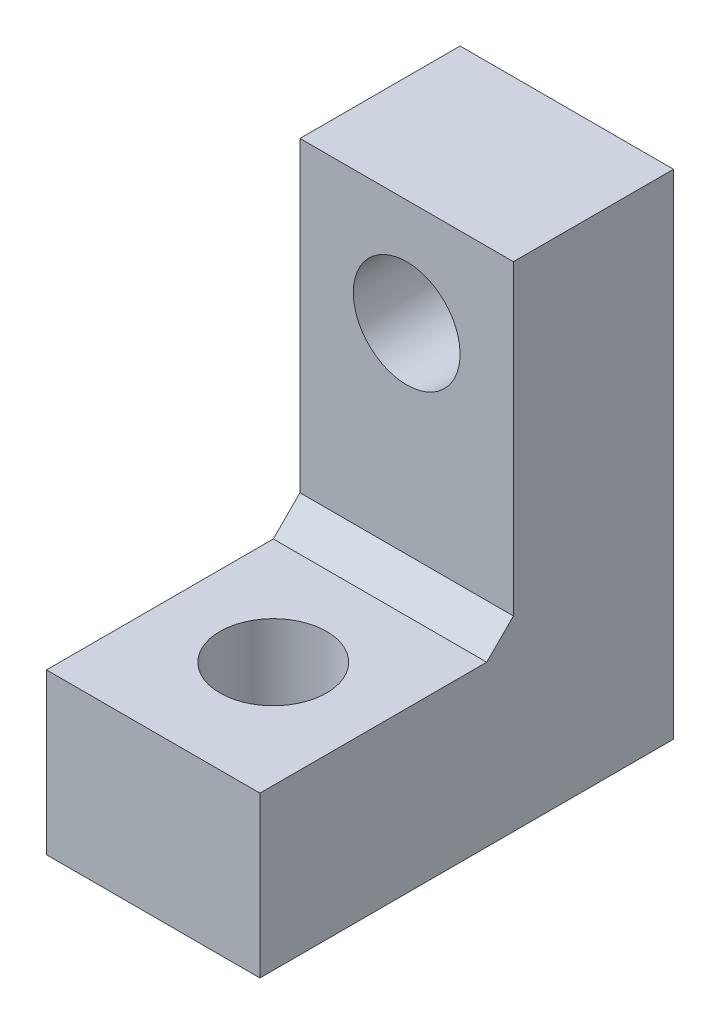
SolidWorks part; units mm, degrees
material "ABS"
ref_plane "Front Plane" through (0, 0, 0) normal (0, 0, 1) x (1, 0, 0)
ref_plane "Top Plane" through (0, 0, 0) normal (0, 1, 0) x (1, 0, 0)
ref_plane "Right Plane" through (0, 0, 0) normal (1, 0, 0) x (0, 0, -1)
sketch "Sketch1" plane through (0, 0, 0) normal (1, 0, 0) x (0, 0, -1)
  line L1 (0, 0) -> (15.5, 0)
  line L2 (0, 0) -> (0, 6)
  line L3 (0, 6) -> (15.5, 6)
  line L4 (15.5, 0) -> (15.5, 6)
  line L5 (15.5, 6) -> (9.5, 6)
  line L6 (15.5, 6) -> (15.5, 18.5)
  line L7 (15.5, 18.5) -> (9.5, 18.5)
  line L8 (9.5, 6) -> (9.5, 18.5)
  dimension "D1" = 6
  dimension "D2" = 6
  dimension "D3" = 18.5
  dimension "D4" = 15.5
extrude "Boss-Extrude1" add sketch "Sketch1" along normal blind 8 contours L8 L3 L6 L7 | L1 L4 L3 L2
chamfer "Chamfer1" distance 1 angle 45 1 edges at (4, 6, -9.5)
sketch "Sketch2" plane through (0, 0, -15.5) normal (0, 0, -1) x (-1, 0, 0)
  line L0 (-4, 18.5) -> (-4, 14.5) construction
  line L1 (-8, 18.5) -> (0, 18.5) construction
  line L2 (-4, 14.5) -> (-4, 4.5) construction
  circle A0 centre (-4, 14.5) radius 2
  circle A1 centre (-4, 4.5) radius 2
  dimension "D1" = 4
  dimension "D2" = 4
  dimension "D3" = 10
  dimension "D4" = 4
extrude "Cut-Extrude1" cut sketch "Sketch2" against normal up to surface (6 mm away) up to face at (4, 12.75, -9.5)
sketch "Sketch3" plane through (0, 6, 0) normal (0, 1, 0) x (1, 0, 0)
  line L0 (8, 0) -> (0, 0) construction
  line L1 (4, 4.5) -> (4, 0) construction
  circle A0 centre (4, 4.5) radius 2
  dimension "D1" = 4
  dimension "D2" = 4.5
extrude "Cut-Extrude2" cut sketch "Sketch3" against normal through all
